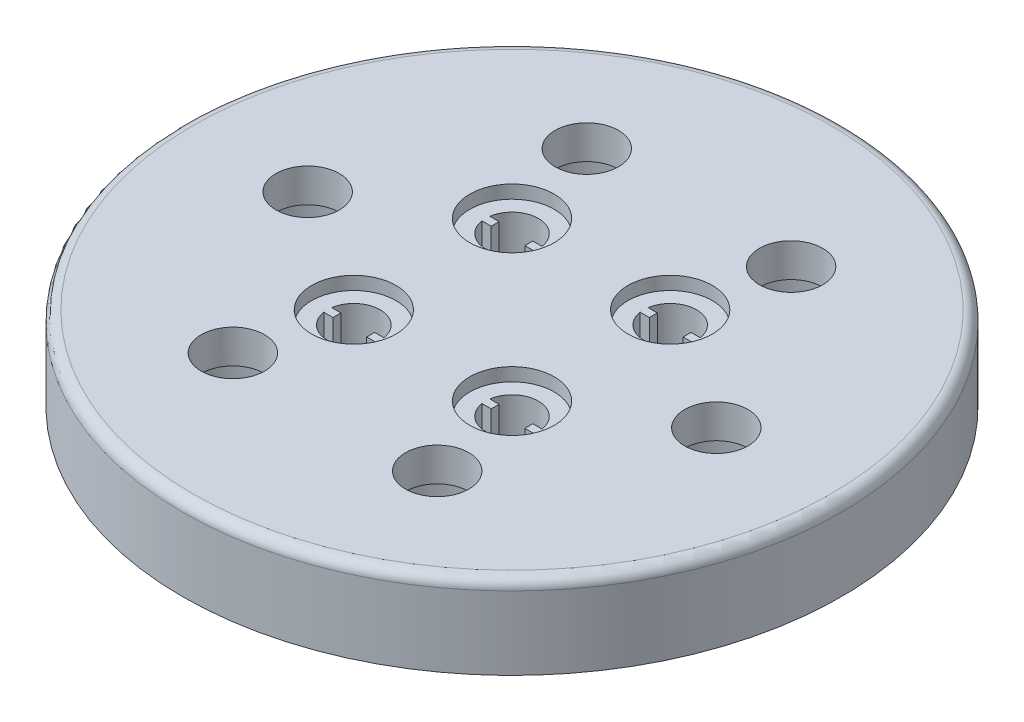
SolidWorks part; units mm, degrees
ref_plane "Front Plane" through (0, 0, 0) normal (0, 0, 1) x (1, 0, 0)
ref_plane "Top Plane" through (0, 0, 0) normal (0, 1, 0) x (1, 0, 0)
ref_plane "Right Plane" through (0, 0, 0) normal (1, 0, 0) x (0, 0, -1)
sketch "Sketch1" plane through (0, 0, 0) normal (0, 1, 0) x (1, 0, 0)
  circle A0 centre (0, 0) radius 25
  dimension "D1" = 50
extrude "Boss-Extrude1" add sketch "Sketch1" along normal blind 6.35
sketch "Sketch3" plane through (0, 0, 0) normal (0, -1, 0) x (1, 0, 0)
  circle A0 centre (-15.5, 0) radius 2.4
  dimension "D2" = 4.8
  dimension "D1" = 15.5
extrude "Cut-Extrude3" cut sketch "Sketch3" against normal through all
sketch "Sketch4" plane through (0, 0, 0) normal (0, -1, 0) x (1, 0, 0)
  circle A0 centre (-15.5, 0) radius 4.65
  dimension "D1" = 9.3
extrude "Cut-Extrude4" cut sketch "Sketch4" against normal blind 3.8
pattern_circular "CirPattern3" count 6 over 360 about axis through (0, 0, 0) along (0, 1, 0) of "Cut-Extrude4", "Cut-Extrude3"
sketch "Sketch5" plane through (0, 0, 0) normal (0, -1, 0) x (1, 0, 0)
  line L0 (0, 0) -> (39.6178, 0) construction
  line L1 (0, 0) -> (0, 34.3235) construction
  circle A0 centre (-6, -6) radius 1.25
  circle A1 centre (6, -6) radius 1.25
  circle A2 centre (-6, 6) radius 1.25
  circle A3 centre (6, 6) radius 1.25
  dimension "D1" = 2.5
  dimension "D2" = 12
  dimension "D3" = 12
extrude "Cut-Extrude5" cut sketch "Sketch5" against normal through all
sketch "Sketch6" plane through (0, 0, 0) normal (0, -1, 0) x (-1, 0, 0)
  circle A0 centre (-6, 6) radius 2.75 construction
  circle A2 centre (-6, 6) radius 3.6 construction
  dimension "D1" = 5.5
  dimension "D2" = 7.2
sketch "Sketch7" plane through (0, 6.35, 0) normal (0, 1, 0) x (1, 0, 0)
  line L0 (3.4663, 6) -> (8.8505, 6) construction
  line L1 (4.0226, 6.3) -> (4.7226, 6.3)
  line L2 (4.7226, 6.3) -> (4.7226, 5.7)
  line L3 (4.7226, 5.7) -> (4.0226, 5.7)
  line L4 (6, 6) -> (6, 8.3524) construction
  line L5 (7.2774, 5.7) -> (7.9774, 5.7)
  line L6 (7.9774, 6.3) -> (7.2774, 6.3)
  line L7 (7.2774, 6.3) -> (7.2774, 5.7)
  line L8 (0, 0) -> (28.5907, 0) construction
  line L9 (0, 0) -> (0, 28.3292) construction
  line L10 (-6, 6) -> (-6, 8.3524) construction
  line L11 (-3.4663, 6) -> (-8.8505, 6) construction
  line L12 (-7.2774, 6.3) -> (-7.2774, 5.7)
  line L13 (-7.9774, 6.3) -> (-7.2774, 6.3)
  line L14 (-7.2774, 5.7) -> (-7.9774, 5.7)
  line L15 (-4.7226, 5.7) -> (-4.0226, 5.7)
  line L16 (-4.7226, 6.3) -> (-4.7226, 5.7)
  line L17 (-4.0226, 6.3) -> (-4.7226, 6.3)
  line L18 (-3.4663, -6) -> (-8.8505, -6) construction
  line L19 (-6, -6) -> (-6, -8.3524) construction
  line L20 (6, -6) -> (6, -8.3524) construction
  line L21 (3.4663, -6) -> (8.8505, -6) construction
  line L22 (-4.0226, -6.3) -> (-4.7226, -6.3)
  line L23 (-4.7226, -6.3) -> (-4.7226, -5.7)
  line L24 (-4.7226, -5.7) -> (-4.0226, -5.7)
  line L25 (-7.2774, -5.7) -> (-7.9774, -5.7)
  line L26 (-7.9774, -6.3) -> (-7.2774, -6.3)
  line L27 (-7.2774, -6.3) -> (-7.2774, -5.7)
  line L28 (7.2774, -6.3) -> (7.2774, -5.7)
  line L29 (7.9774, -6.3) -> (7.2774, -6.3)
  line L30 (7.2774, -5.7) -> (7.9774, -5.7)
  line L31 (4.7226, -5.7) -> (4.0226, -5.7)
  line L32 (4.7226, -6.3) -> (4.7226, -5.7)
  line L33 (4.0226, -6.3) -> (4.7226, -6.3)
  arc A0 (4.0226, 5.7) -> (7.9774, 5.7) centre (6, 6) ccw
  arc A1 (-7.9774, 6.3) -> (-4.0226, 6.3) centre (-6, 6) cw
  arc A2 (-4.0226, 5.7) -> (-7.9774, 5.7) centre (-6, 6) cw
  arc A3 (7.9774, -6.3) -> (4.0226, -6.3) centre (6, -6) cw
  arc A4 (7.9774, 6.3) -> (4.0226, 6.3) centre (6, 6) ccw
  arc A5 (-4.0226, -5.7) -> (-7.9774, -5.7) centre (-6, -6) ccw
  arc A6 (-7.9774, -6.3) -> (-4.0226, -6.3) centre (-6, -6) ccw
  arc A7 (4.0226, -5.7) -> (7.9774, -5.7) centre (6, -6) cw
  dimension "D1" = 4
  dimension "D2" = 0.6
  dimension "D3" = 0.7
extrude "Cut-Extrude6" cut sketch "Sketch7" against normal through all
sketch "Sketch8" plane through (0, 6.35, 0) normal (0, 1, 0) x (1, 0, 0)
  circle A0 centre (6, -6) radius 3.2
  circle A1 centre (6, 6) radius 3.2
  circle A2 centre (-6, 6) radius 3.2
  circle A3 centre (-6, -6) radius 3.2
  dimension "D1" = 6.4
extrude "Cut-Extrude7" cut sketch "Sketch8" against normal blind 1
sketch "Sketch9" plane through (0, 5.35, 0) normal (0, 1, 0) x (1, 0, 0)
  circle A0 centre (6, 6) radius 2
  circle A1 centre (-6, 6) radius 2
  circle A2 centre (6, -6) radius 2
  circle A3 centre (-6, -6) radius 2
  arc A4 (4.0226, 5.7) -> (7.9774, 5.7) centre (6, 6) ccw construction
  arc A5 (4.0226, -6.3) -> (7.9774, -6.3) centre (6, -6) ccw construction
  arc A6 (-7.9774, -6.3) -> (-4.0226, -6.3) centre (-6, -6) ccw construction
  arc A7 (-7.9774, 5.7) -> (-4.0226, 5.7) centre (-6, 6) ccw construction
fillet "Fillet1" radius 0.8 1 edges at (0, 6.35, 25)
